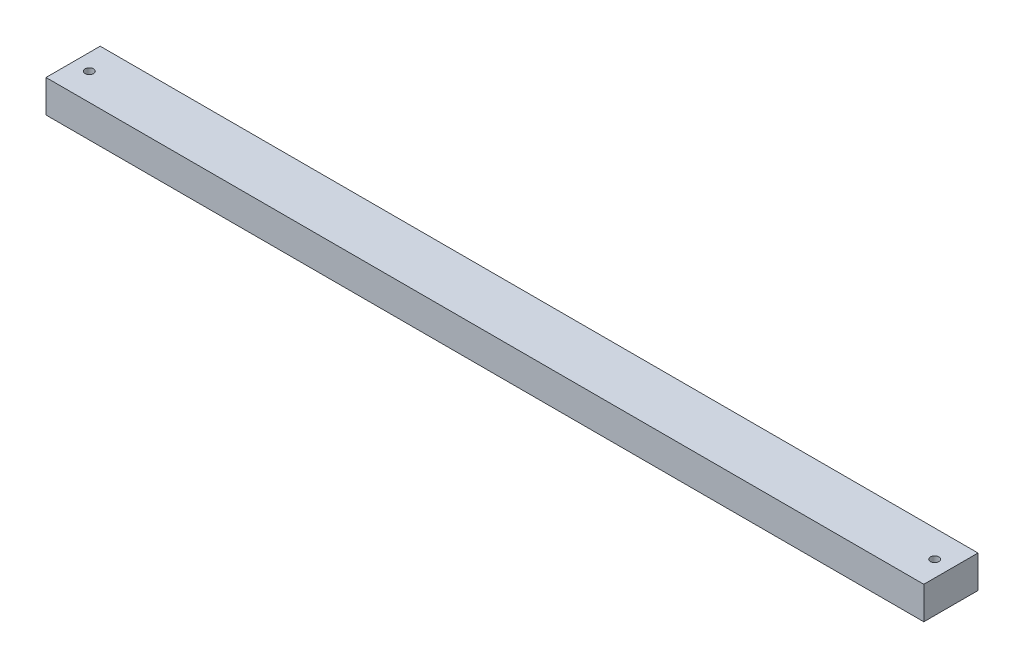
SolidWorks part; units mm, degrees
ref_plane "Front Plane" through (0, 0, 0) normal (0, 0, 1) x (1, 0, 0)
ref_plane "Top Plane" through (0, 0, 0) normal (0, 1, 0) x (1, 0, 0)
ref_plane "Right Plane" through (0, 0, 0) normal (1, 0, 0) x (0, 0, -1)
sketch "Sketch1" plane through (0, 0, 0) normal (0, 1, 0) x (1, 0, 0)
  line L1 (-162, 10) -> (162, 10)
  line L2 (-162, 10) -> (-162, -10)
  line L3 (-162, -10) -> (162, -10)
  line L4 (162, 10) -> (162, -10)
  line L5 (-162, 10) -> (162, -10) construction
  line L6 (-162, -10) -> (162, 10) construction
  point P0 (0, 0)
  dimension "D1" = 324
  dimension "D2" = 20
extrude "Boss-Extrude1" add sketch "Sketch1" along normal blind 12
sketch "Sketch2" plane through (0, 12, 0) normal (0, 1, 0) x (1, 0, 0)
  line L0 (-162, 10) -> (-162, -10) construction
  line L1 (162, -10) -> (162, 10) construction
  line L2 (162, 10) -> (-162, 10) construction
  circle A0 centre (-156, 0) radius 1.55
  circle A1 centre (156, 0) radius 1.55
  point P4 (-162, 0)
  point P7 (162, 0)
  dimension "D1" = 3.1
  dimension "D2" = 3.1
  dimension "D3" = 6
  dimension "D4" = 6
  dimension "D5" = 10
  dimension "D6" = 10
extrude "Cut-Extrude1" cut sketch "Sketch2" against normal through all
